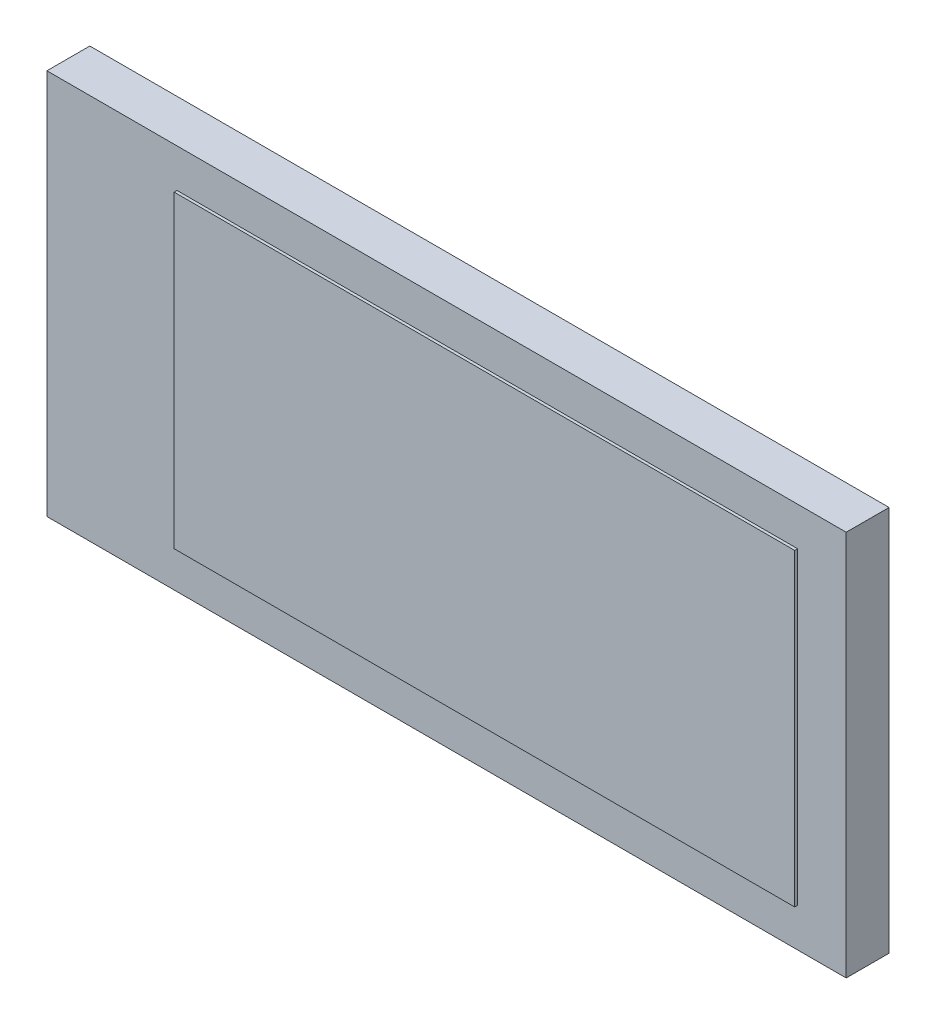
SolidWorks part; units mm, degrees
ref_plane "前视基准面" through (0, 0, 0) normal (0, 0, 1) x (1, 0, 0)
ref_plane "上视基准面" through (0, 0, 0) normal (0, 1, 0) x (1, 0, 0)
ref_plane "右视基准面" through (0, 0, 0) normal (1, 0, 0) x (0, 0, -1)
sketch "草图1" plane through (0, 0, 0) normal (0, 0, 1) x (1, 0, 0)
  line L1 (0, 0) -> (27.95, 0)
  line L2 (0, 0) -> (0, -13.5)
  line L3 (0, -13.5) -> (27.95, -13.5)
  line L4 (27.95, 0) -> (27.95, -13.5)
  point P5 (0, 0)
  point P6 (0, 0)
  point P7 (0, 0)
  point P8 (0, 0)
  point P9 (0, 0)
extrude "凸台-拉伸1" add sketch "草图1" along normal blind 1.5
sketch "草图2" plane through (0, 0, 1.5) normal (0, 0, 1) x (1, 0, 0)
  line L2 (0, -6.75) -> (26.25, -6.75) construction
  line L3 (0, 0) -> (0, -13.5) construction
  line L4 (27.95, -13.5) -> (27.95, 0) construction
  line L6 (26.25, -12.15) -> (26.25, -1.35)
  line L7 (27.95, -0.35) -> (3.35, -0.35)
  line L8 (27.95, -0.35) -> (27.95, -13.15)
  line L9 (27.95, -13.15) -> (3.35, -13.15)
  line L10 (3.35, -0.35) -> (3.35, -13.15)
  line L14 (4.55, -12.15) -> (26.25, -12.15)
  line L15 (26.25, -13.15) -> (26.25, -0.35) construction
  line L17 (4.55, -12.15) -> (4.55, -1.35)
  line L18 (4.55, -13.15) -> (4.55, -0.35) construction
  line L19 (4.55, -1.35) -> (26.25, -1.35)
  dimension "D3" = 21.7
extrude "凸台-拉伸2" add sketch "草图2" along normal blind 0.1 contours L17 L19 L6 L14
